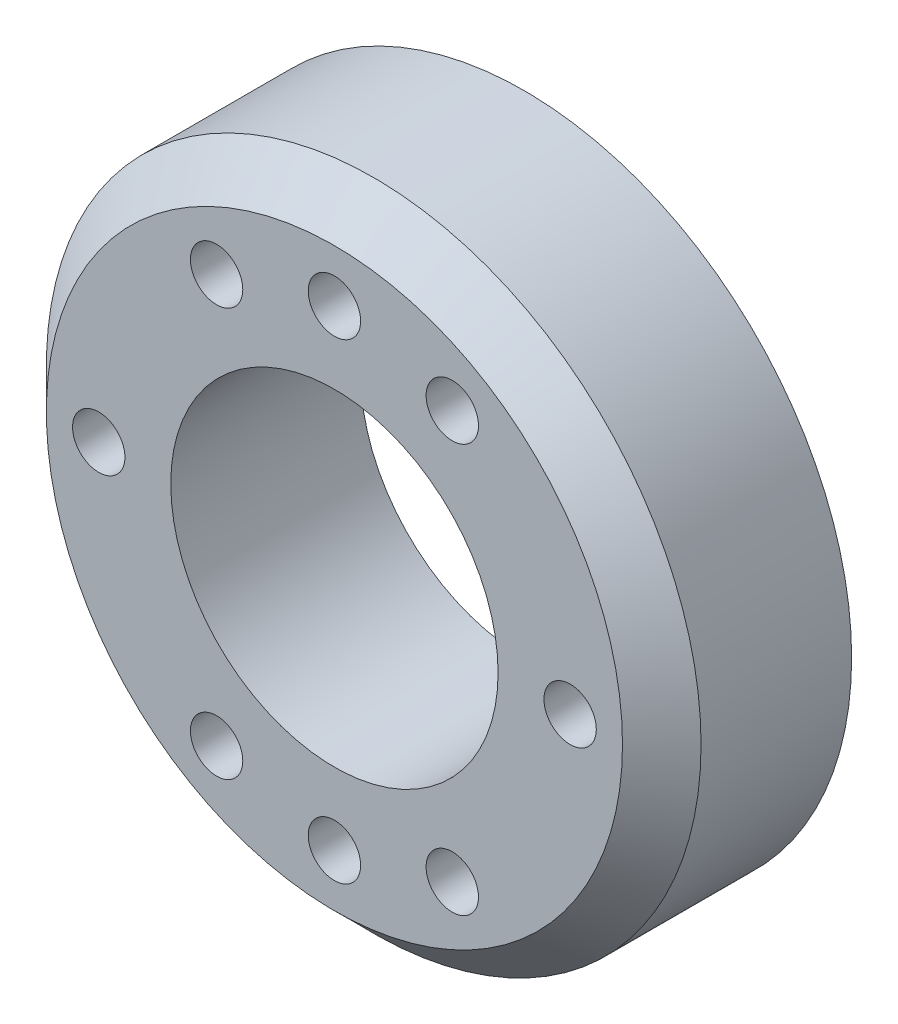
SolidWorks part; units mm, degrees
material "ABS PC"
ref_plane "Front Plane" through (0, 0, 0) normal (0, 0, 1) x (1, 0, 0)
ref_plane "Top Plane" through (0, 0, 0) normal (0, 1, 0) x (1, 0, 0)
ref_plane "Right Plane" through (0, 0, 0) normal (1, 0, 0) x (0, 0, -1)
sketch "Sketch1" plane through (0, 0, 0) normal (0, 0, 1) x (1, 0, 0)
  circle A0 centre (0, 0) radius 25
  circle A1 centre (0, 0) radius 12.5
  circle A2 centre (0, 0) radius 18 construction
  circle A3 centre (0, 18) radius 2
  circle A4 centre (9, 15.5885) radius 2
  circle A6 centre (18, 0) radius 2
  circle A8 centre (9, -15.5885) radius 2
  circle A9 centre (0, -18) radius 2
  circle A10 centre (-9, -15.5885) radius 2
  circle A12 centre (-18, 0) radius 2
  circle A14 centre (-9, 15.5885) radius 2
  circle A15 centre (-15.5885, 9) radius 2 [skipped]
  circle A16 centre (15.5885, 9) radius 2 [skipped]
  circle A17 centre (-15.5885, -9) radius 2 [skipped]
  circle A18 centre (15.5885, -9) radius 2 [skipped]
  point P19 (0, 0)
  dimension "D1" = 25
  dimension "D2" = 50
  dimension "D3" = 36
  dimension "D4" = 4
  dimension "D5" = 12
extrude "Boss-Extrude1" add sketch "Sketch1" along normal blind 14.5
fillet "Fillet1" [suppressed] radius 2
fillet "Fillet2" [suppressed] radius 1
fillet "Fillet3" [suppressed] radius 0.5
chamfer "Chamfer1" distance 3 angle 45 1 edges at (25, 0, 14.5)
